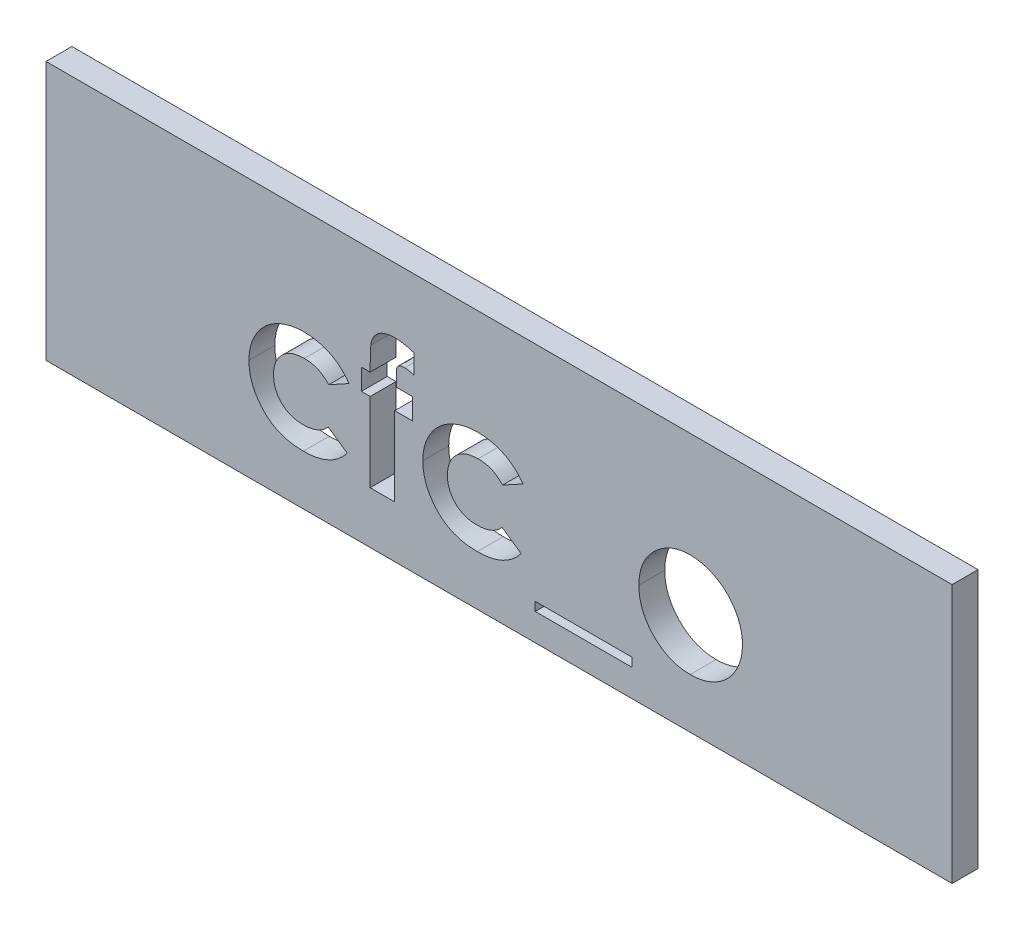
SolidWorks part; units mm, degrees
ref_plane "Plan de face" through (0, 0, 0) normal (0, 0, 1) x (1, 0, 0)
ref_plane "Plan de dessus" through (0, 0, 0) normal (0, 1, 0) x (1, 0, 0)
ref_plane "Plan de droite" through (0, 0, 0) normal (1, 0, 0) x (0, 0, -1)
sketch "Esquisse1" plane through (0, 0, 0) normal (0, 0, 1) x (1, 0, 0)
  line L1 (0, 0) -> (35, 0)
  line L2 (0, 0) -> (0, -10)
  line L3 (0, -10) -> (35, -10)
  line L4 (35, 0) -> (35, -10)
  dimension "D1" = 35
  dimension "D2" = 10
extrude "Boss.-Extru.1" add sketch "Esquisse1" along normal blind 1
sketch "Esquisse2" plane through (0, 0, 0) normal (0, 0, -1) x (-1, 0, 0)
  line L0 (-35, 0) -> (0, 0) construction
  line L1 (-35, -10) -> (-35, 0) construction
  line L2 (0, 0) -> (0, -10) construction
  circle A0 centre (-30, -5) radius 1
  circle A1 centre (-5, -5) radius 1
  dimension "D4" = 2
  dimension "D1" = 5
  dimension "D2" = 5
  dimension "D3" = 5
extrude "Boss.-Extru.2" add sketch "Esquisse2" along normal blind 3
chamfer "Chanfrein1" distance 0.5 angle 45 2 edges at (29, -5, -3) (4, -5, -3)
sketch "Esquisse3" plane through (0, 0, 1) normal (0, 0, 1) x (1, 0, 0)
  line L0 (7.5, -8) -> (27.5, -8) construction
  line L3 (0, -10) -> (35, -10) construction
  line L4 (0, 0) -> (0, -10) construction
  line L5 (35, -10) -> (35, 0) construction
  text T1 "<b>cfc_o</b>" font "Century Gothic" height in points 20
  point P12 (27.5, -8)
  dimension "D1" = 2
  dimension "D2" = 7.5
  dimension "D3" = 20
  dimension "D4" = 7.5
extrude "Enlèv. mat.-Extru.2" cut sketch "Esquisse3" against normal blind 1
